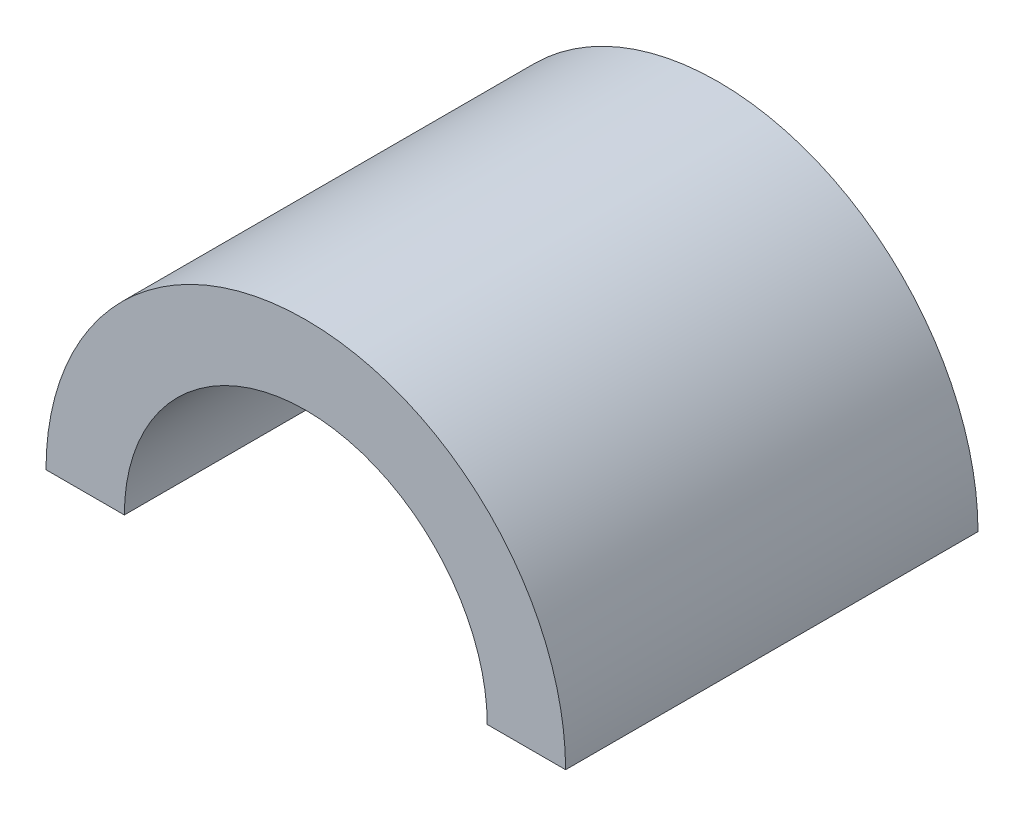
SolidWorks part; units mm, degrees
other "Markup1"
sketch "Sketch2" plane through (-16.002, 0, 25.4) normal (-0.3063, -0.9021, 0.3041) x (0.6821, 0.0148, 0.7311)
material "Natural Rubber"
ref_plane "Front Plane" through (0, 0, 0) normal (0, 0, 1) x (1, 0, 0)
ref_plane "Top Plane" through (0, 0, 0) normal (0, 1, 0) x (1, 0, 0)
ref_plane "Right Plane" through (0, 0, 0) normal (1, 0, 0) x (0, 0, -1)
sketch "Sketch1" plane through (0, 0, 0) normal (0, 0, 1) x (1, 0, 0)
  line L0 (-16.002, 0) -> (-11.176, 0)
  line L1 (11.176, 0) -> (16.002, 0)
  line L2 (-11.176, 0) -> (11.176, 0) construction
  arc A0 (11.176, 0) -> (-11.176, 0) centre (0, 0) ccw
  arc A1 (16.002, 0) -> (-16.002, 0) centre (0, 0) ccw
  dimension "D2" = 22.352
  dimension "D1" = 4.826
extrude "Boss-Extrude1" add sketch "Sketch1" along normal blind 25.4
